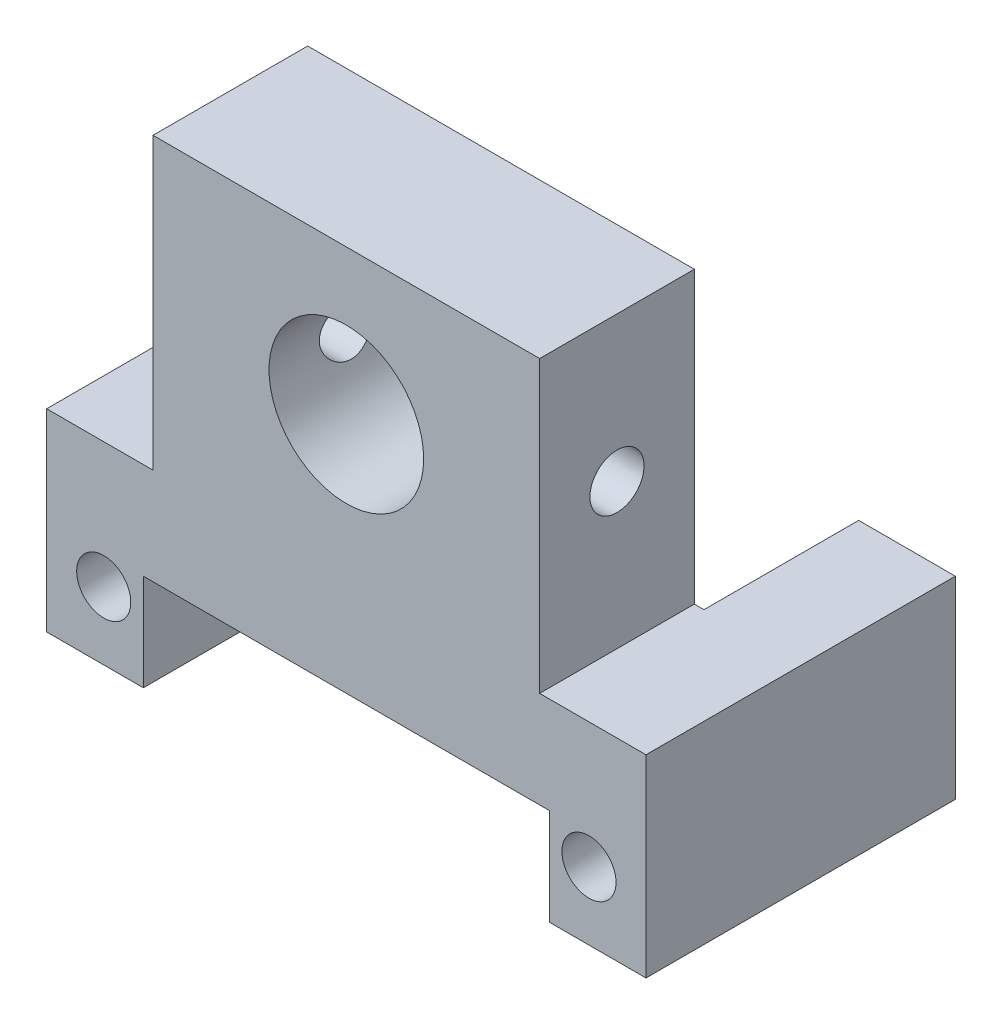
SolidWorks part; units mm, degrees
ref_plane "Plan de face" through (0, 0, 0) normal (0, 0, 1) x (1, 0, 0)
ref_plane "Plan de dessus" through (0, 0, 0) normal (0, 1, 0) x (1, 0, 0)
ref_plane "Plan de droite" through (0, 0, 0) normal (1, 0, 0) x (0, 0, -1)
sketch "Esquisse1" plane through (0, 0, 0) normal (0, 0, 1) x (1, 0, 0)
  line L0 (-32.764, 3.5) -> (28.0862, 3.5) construction
  line L1 (-10.5, -5) -> (10.5, -5) construction
  line L2 (-10.5, -5) -> (-10.5, 5) construction
  line L3 (-10.5, 5) -> (10.5, 5) construction
  line L4 (10.5, -5) -> (10.5, 5) construction
  line L5 (-10.5, -5) -> (10.5, 5) construction
  line L6 (-10.5, 5) -> (10.5, -5) construction
  line L7 (0, 0) -> (0, 18.1795) construction
  line L8 (15.5, 10) -> (-15.5, 10)
  line L9 (10.5, 0) -> (15.5, 0)
  line L10 (10.5, 0) -> (10.5, 5)
  line L11 (10.5, 5) -> (-10.5, 5)
  line L12 (15.5, 0) -> (15.5, 10)
  line L13 (-10.5, 0) -> (-15.5, 0)
  line L14 (-15.5, 0) -> (-15.5, 10)
  line L15 (-10.5, 0) -> (-10.5, 5)
  circle A0 centre (12.55, 3.5) radius 1.4
  circle A1 centre (-12.55, 3.5) radius 1.4
  point P0 (0, 0)
  point P19 (0, 10)
  point P22 (0, 5)
  dimension "D3" = 12.55
  dimension "D5" = 5
  dimension "D1" = 21
  dimension "D2" = 10
  dimension "D4" = 1.5
  dimension "D6" = 10
extrude "Boss.-Extru.1" add sketch "Esquisse1" along normal blind 16
sketch "Esquisse2" plane through (0, 10, 0) normal (0, 1, 0) x (1, 0, 0)
  line L0 (0, -16) -> (0, 0) construction
  line L1 (-15.5, 0) -> (15.5, 0) construction
  line L2 (-15.5, 0) -> (-15.5, -16) construction
  line L3 (-15.5, -16) -> (15.5, -16) construction
  line L4 (15.5, 0) -> (15.5, -16) construction
  line L5 (10, -16) -> (10, 0)
  line L6 (10, -16) -> (-10, -16)
  line L8 (10, 0) -> (-10, 0)
  line L9 (-10, -16) -> (-10, 0)
  dimension "D1" = 10
extrude "Boss.-Extru.2" add sketch "Esquisse2" along normal blind 15
sketch "Esquisse3" plane through (0, 0, 16) normal (0, 0, 1) x (1, 0, 0)
  line L0 (-10, 10) -> (10, 10) construction
  line L1 (0, 10) -> (0, 25) construction
  line L2 (-10, 25) -> (10, 25) construction
  circle A0 centre (0, 17.5) radius 4
  dimension "D1" = 7.5
extrude "Enlèv. mat.-Extru.1" cut sketch "Esquisse3" against normal blind 15 contours A0
sketch "Esquisse4" plane through (0, 5, 0) normal (0, -1, 0) x (1, 0, 0)
  line L0 (10.5, 16) -> (10.5, 0) construction
  line L1 (-10.5, 0) -> (10.5, 0)
  line L2 (-10.5, 0) -> (-10.5, 8)
  line L3 (-10.5, 8) -> (10.5, 8)
  line L4 (10.5, 0) -> (10.5, 8)
extrude "Enlèv. mat.-Extru.2" cut sketch "Esquisse4" against normal blind 21
sketch "Esquisse5" plane through (-10, 0, 0) normal (-1, 0, 0) x (0, 0, 1)
  line L0 (12, 25) -> (12, 10) construction
  line L1 (8, 25) -> (16, 25) construction
  line L2 (8, 10) -> (16, 10) construction
  circle A0 centre (12, 17.5) radius 1.4
  dimension "D1" = 7.5
extrude "Enlèv. mat.-Extru.3" cut sketch "Esquisse5" against normal blind 21
